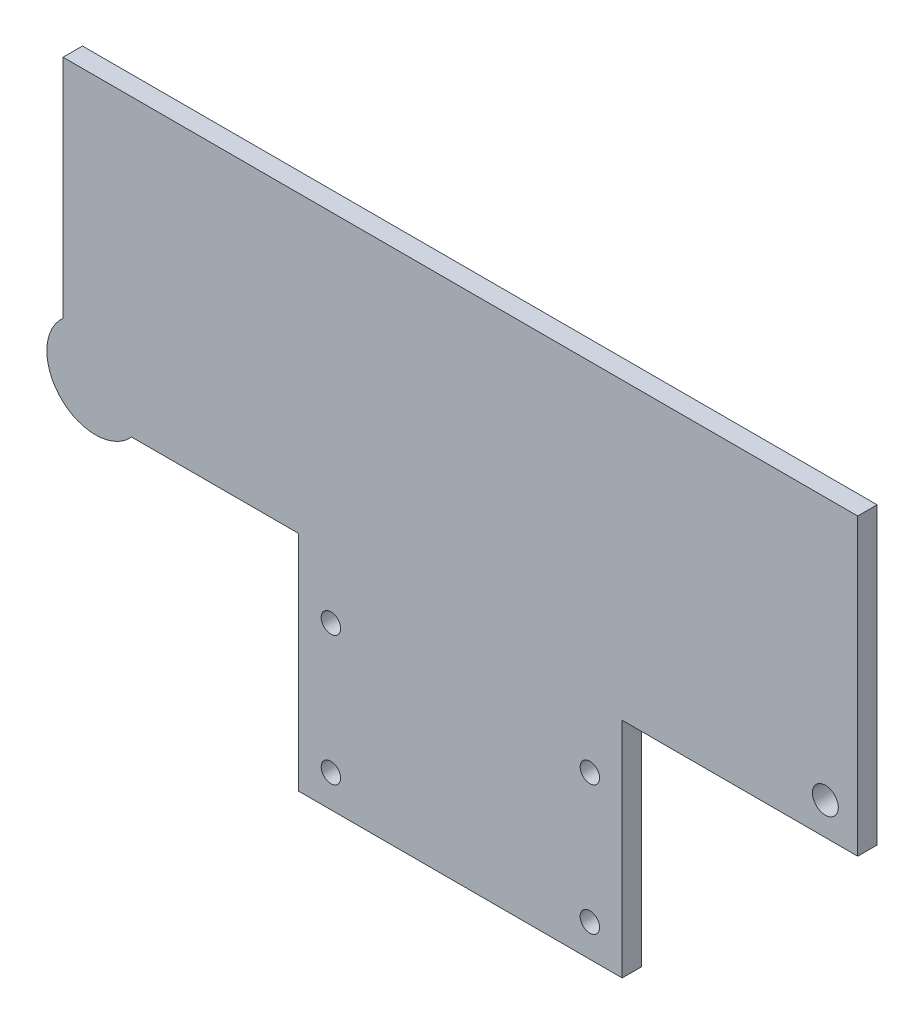
SolidWorks part; units mm, degrees
ref_plane "Plan de face" through (0, 0, 0) normal (0, 0, 1) x (1, 0, 0)
ref_plane "Plan de dessus" through (0, 0, 0) normal (0, 1, 0) x (1, 0, 0)
ref_plane "Plan de droite" through (0, 0, 0) normal (1, 0, 0) x (0, 0, -1)
sketch "Esquisse1" plane through (0, 0, 0) normal (0, 0, 1) x (1, 0, 0)
  line L0 (-25, 0) -> (25, 0) construction
  line L1 (-61.3816, 0) -> (61.3816, 0)
  line L2 (25, -80) -> (25, -45.5212)
  line L4 (25, -80) -> (-25, -80)
  line L5 (-25, -50) -> (25, -50) construction
  line L6 (-25, -65) -> (25, -65) construction
  line L7 (-25, -80) -> (-25, -45.5212)
  line L8 (0, 0) -> (0, -80) construction
  line L15 (61.3816, 0) -> (25, 0) construction
  line L17 (-25, -45.5212) -> (-25, 0) construction
  line L18 (-61.3816, 0) -> (-61.3816, -45.5212)
  line L19 (-61.3816, -45.5212) -> (-25, -45.5212)
  line L20 (0, -20) -> (-25, -20) construction
  line L21 (25, -45.5212) -> (25, 0) construction
  line L22 (61.3816, 0) -> (61.3816, -45.5212)
  line L23 (61.3816, -45.5212) -> (25, -45.5212)
  line L24 (0, -20) -> (-56.3816, -40.5212) construction
  circle A1 centre (0, -20) radius 2
  circle A3 centre (-20, -55) radius 1.5
  circle A4 centre (20, -55) radius 1.5
  circle A5 centre (20, -75) radius 1.5
  circle A6 centre (-20, -75) radius 1.5
  circle A15 centre (56.3816, -40.5212) radius 2
  circle A17 centre (-56.3816, -40.5212) radius 2
  point P0 (0, 0)
  point P2 (0, 0)
  dimension "D4" = 4
  dimension "D13" = 3
  dimension "D14" = 20
  dimension "D22" = 5
  dimension "D23" = 5
  dimension "D24" = 60
  dimension "D25" = 20
  dimension "D26" = 4
  dimension "D27" = 25
  dimension "D6" = 20
  dimension "D9" = 80
  dimension "D11" = 30
  dimension "D12" = 15
  dimension "D15" = 10
extrude "Boss.-Extru.1" add sketch "Esquisse1" along normal blind 3
sketch "Esquisse3" plane through (0, 0, 0) normal (0, 0, -1) x (-1, 0, 0)
  circle A1 centre (56.3816, -40.5212) radius 7.5
  circle A2 centre (0, -20) radius 7.5
  dimension "D2" = 15
  dimension "D3" = 15
extrude "Boss.-Extru.2" add sketch "Esquisse3" along normal blind 6 from offset 3
sketch "Esquisse4" plane through (0, 0, -3) normal (0, 0, -1) x (-1, 0, 0)
  circle A0 centre (56.3816, -40.5212) radius 3.875
  circle A2 centre (0, -20) radius 3.875
  dimension "D1" = 7.75
  dimension "D3" = 7.75
extrude "Enlèv. mat.-Extru.1" cut sketch "Esquisse4" against normal blind 1
sketch "Esquisse5" plane through (0, 0, -2) normal (0, 0, -1) x (-1, 0, 0)
  circle A0 centre (56.3816, -40.5212) radius 2.375
  circle A2 centre (0, -20) radius 2.375
  dimension "D1" = 4.75
  dimension "D3" = 4.75
extrude "Enlèv. mat.-Extru.2" cut sketch "Esquisse5" against normal blind 4
